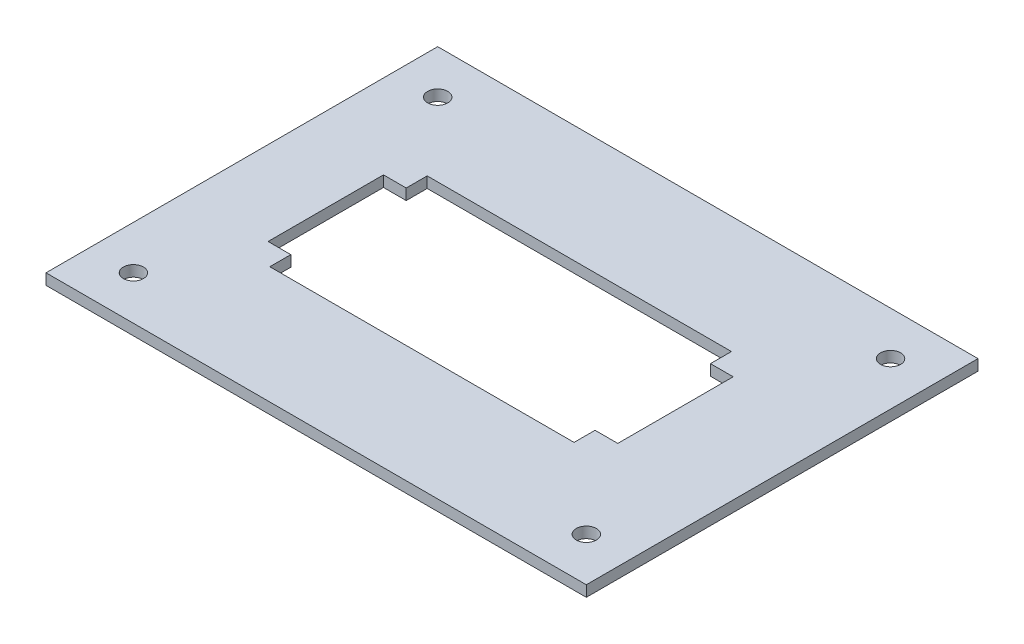
SolidWorks part; units mm, degrees
ref_plane "Front Plane" through (0, 0, 0) normal (0, 0, 1) x (1, 0, 0)
ref_plane "Top Plane" through (0, 0, 0) normal (0, 1, 0) x (1, 0, 0)
ref_plane "Right Plane" through (0, 0, 0) normal (1, 0, 0) x (0, 0, -1)
sketch "Sketch2" plane through (0, 0, 0) normal (0, 1, 0) x (1, 0, 0)
  line L0 (15.494, 39.878) -> (59.69, 39.878)
  line L1 (0, 0) -> (78.486, 0)
  line L2 (0, 0) -> (0, 56.896)
  line L3 (0, 56.896) -> (78.486, 56.896)
  line L4 (78.486, 0) -> (78.486, 56.896)
  line L5 (59.69, 39.878) -> (59.69, 36.83)
  line L6 (59.69, 36.83) -> (62.992, 36.83)
  line L7 (62.992, 36.83) -> (62.992, 20.066)
  line L8 (62.992, 20.066) -> (59.69, 20.066)
  line L9 (59.69, 20.066) -> (59.69, 17.018)
  line L10 (59.69, 17.018) -> (15.494, 17.018)
  line L11 (15.494, 17.018) -> (15.494, 20.066)
  line L12 (15.494, 20.066) -> (12.192, 20.066)
  line L13 (12.192, 20.066) -> (12.192, 36.83)
  line L14 (12.192, 36.83) -> (15.494, 36.83)
  line L15 (15.494, 36.83) -> (15.494, 39.878)
  point P7 (15.494, 18.542)
  point P18 (59.69, 38.354)
  dimension "D1" = 56.896
  dimension "D2" = 78.486
  dimension "D3" = 12.192
  dimension "D4" = 15.494
  dimension "D5" = 15.494
  dimension "D6" = 17.018
  dimension "D7" = 17.018
  dimension "D8" = 20.066
  dimension "D9" = 20.066
  dimension "D10" = 18.796
  dimension "D11" = 18.796
  dimension "D12" = 15.494
  dimension "D13" = 20.066
  dimension "D14" = 20.066
extrude "Boss-Extrude1" add sketch "Sketch2" along normal blind 1.5875
sketch "Sketch3" plane through (0, 1.5875, 0) normal (0, 1, 0) x (1, 0, 0)
  line L0 (78.486, 56.896) -> (0, 56.896) construction
  line L1 (0, 56.896) -> (0, 0) construction
  line L2 (0, 0) -> (78.486, 0) construction
  line L3 (78.486, 0) -> (78.486, 56.896) construction
  circle A0 centre (6.35, 50.546) radius 1.4605
  circle A1 centre (6.35, 6.35) radius 1.4605
  circle A2 centre (72.136, 50.546) radius 1.4605
  circle A3 centre (72.136, 6.35) radius 1.4605
  dimension "D1" = 2.921
  dimension "D2" = 2.921
  dimension "D3" = 2.921
  dimension "D4" = 2.921
  dimension "D5" = 6.35
  dimension "D6" = 6.35
  dimension "D7" = 6.35
  dimension "D8" = 6.35
  dimension "D9" = 6.35
  dimension "D10" = 6.35
  dimension "D11" = 6.35
  dimension "D12" = 6.35
extrude "Cut-Extrude1" cut sketch "Sketch3" against normal through all
